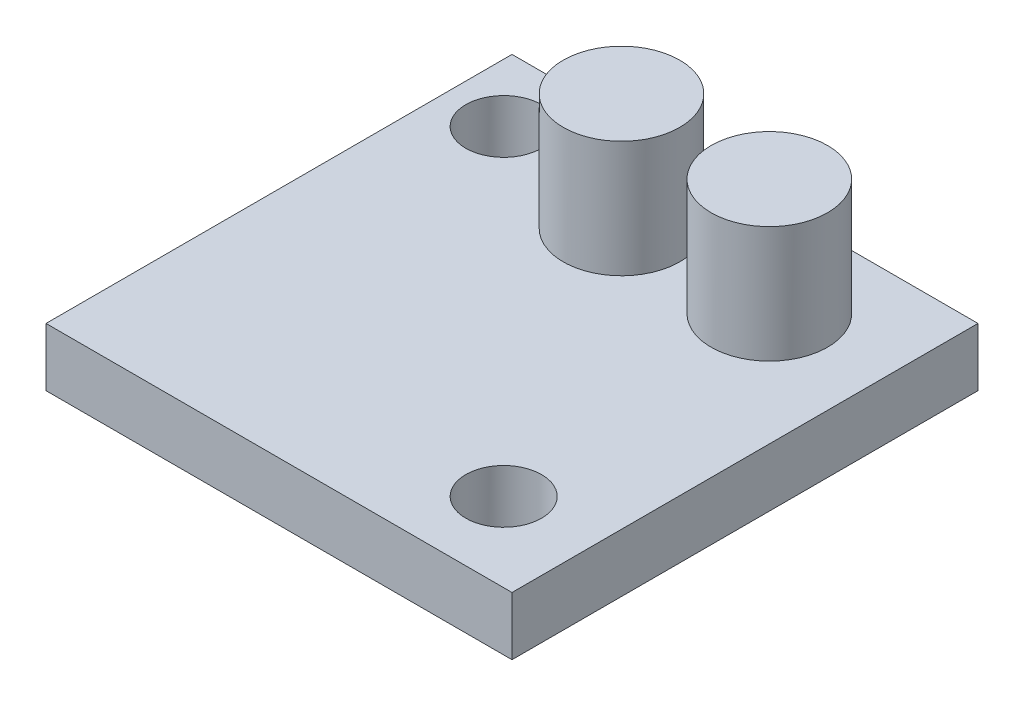
SolidWorks part; units mm, degrees
material "6061-T6 (SS)"
ref_plane "Front Plane" through (0, 0, 0) normal (0, 0, 1) x (1, 0, 0)
ref_plane "Top Plane" through (0, 0, 0) normal (0, 1, 0) x (1, 0, 0)
ref_plane "Right Plane" through (0, 0, 0) normal (1, 0, 0) x (0, 0, -1)
sketch "Sketch1" plane through (0, 0, 0) normal (0, 1, 0) x (1, 0, 0)
  line L1 (0, 0) -> (20.32, 0)
  line L2 (0, 0) -> (0, 20.32)
  line L3 (0, 20.32) -> (20.32, 20.32)
  line L4 (20.32, 0) -> (20.32, 20.32)
extrude "Boss-Extrude1" add sketch "Sketch1" along normal blind 2.54
sketch "Sketch2" plane through (0, 2.54, 0) normal (0, 1, 0) x (1, 0, 0)
  line L1 (0, 20.32) -> (0, 0) construction
  circle A0 centre (2.54, 17.4166) radius 1.651
  circle A1 centre (16.51, 3.4466) radius 1.651
  dimension "D1" = 3.302
  dimension "D2" = 3.302
  dimension "D4" = 2.54
  dimension "D5" = 13.97
  dimension "D3" = 13.97
extrude "Cut-Extrude1" cut sketch "Sketch2" against normal up to next
sketch "Sketch3" plane through (0, 2.54, 0) normal (0, 1, 0) x (1, 0, 0)
  circle A0 centre (8.9534, 16.1411) radius 2.54
  circle A1 centre (15.3999, 16.1411) radius 2.54
  dimension "D1" = 5.08
  dimension "D2" = 5.08
extrude "Boss-Extrude2" add sketch "Sketch3" along normal blind 5.08
